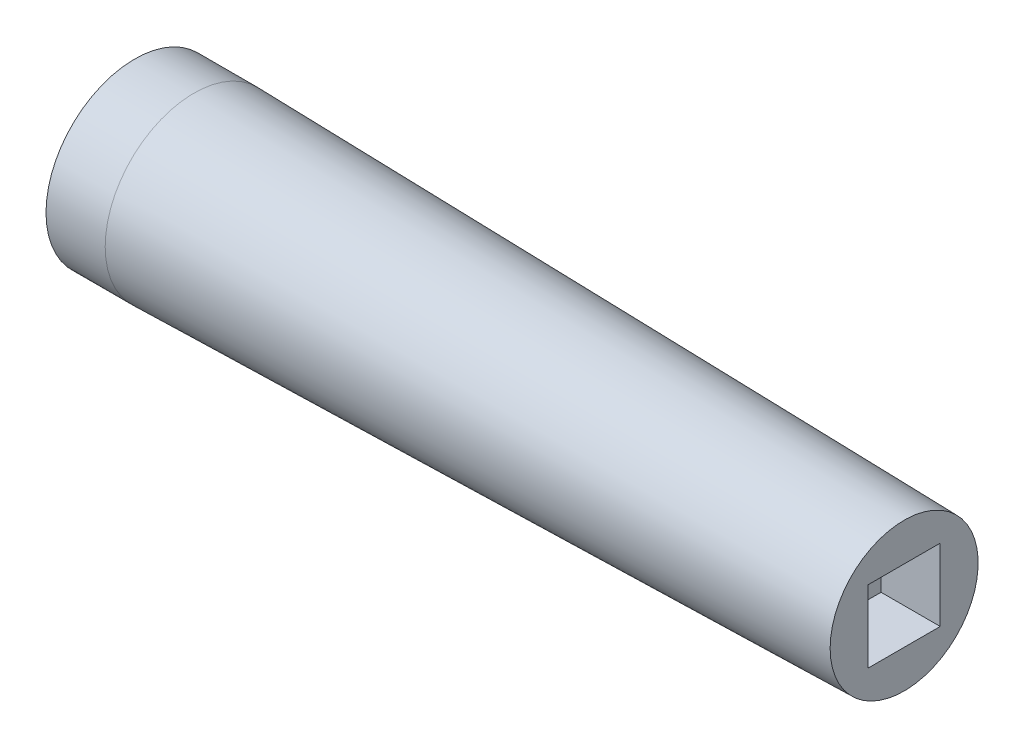
SolidWorks part; units mm, degrees
ref_plane "Front Plane" through (0, 0, 0) normal (0, 0, 1) x (1, 0, 0)
ref_plane "Top Plane" through (0, 0, 0) normal (0, 1, 0) x (1, 0, 0)
ref_plane "Right Plane" through (0, 0, 0) normal (1, 0, 0) x (0, 0, -1)
sketch "Sketch1" plane through (0, 0, 0) normal (0, 1, 0) x (1, 0, 0)
  line L0 (0, 0) -> (165.1, 0)
  line L1 (165.1, 0) -> (165.1, 15.88)
  line L2 (165.1, 15.88) -> (12.7, 19.05)
  line L3 (12.7, 19.05) -> (0, 19.05)
  line L4 (0, 19.05) -> (0, 0)
  dimension "D1" = 165.1
  dimension "D2" = 15.88
  dimension "D3" = 12.7
  dimension "D4" = 19.05
revolve "Revolve1" add sketch "Sketch1" angle 360 about L0
sketch "Sketch2" plane through (165.1, 0, 0) normal (1, 0, 0) x (0, 0, -1)
  line L1 (-7.745, -7.745) -> (7.745, -7.745)
  line L2 (-7.745, -7.745) -> (-7.745, 7.745)
  line L3 (-7.745, 7.745) -> (7.745, 7.745)
  line L4 (7.745, -7.745) -> (7.745, 7.745)
  line L5 (-7.745, -7.745) -> (7.745, 7.745) construction
  line L6 (-7.745, 7.745) -> (7.745, -7.745) construction
  point P0 (0, 0)
  dimension "D1" = 15.49
extrude "Cut-Extrude1" cut sketch "Sketch2" against normal blind 12.7
